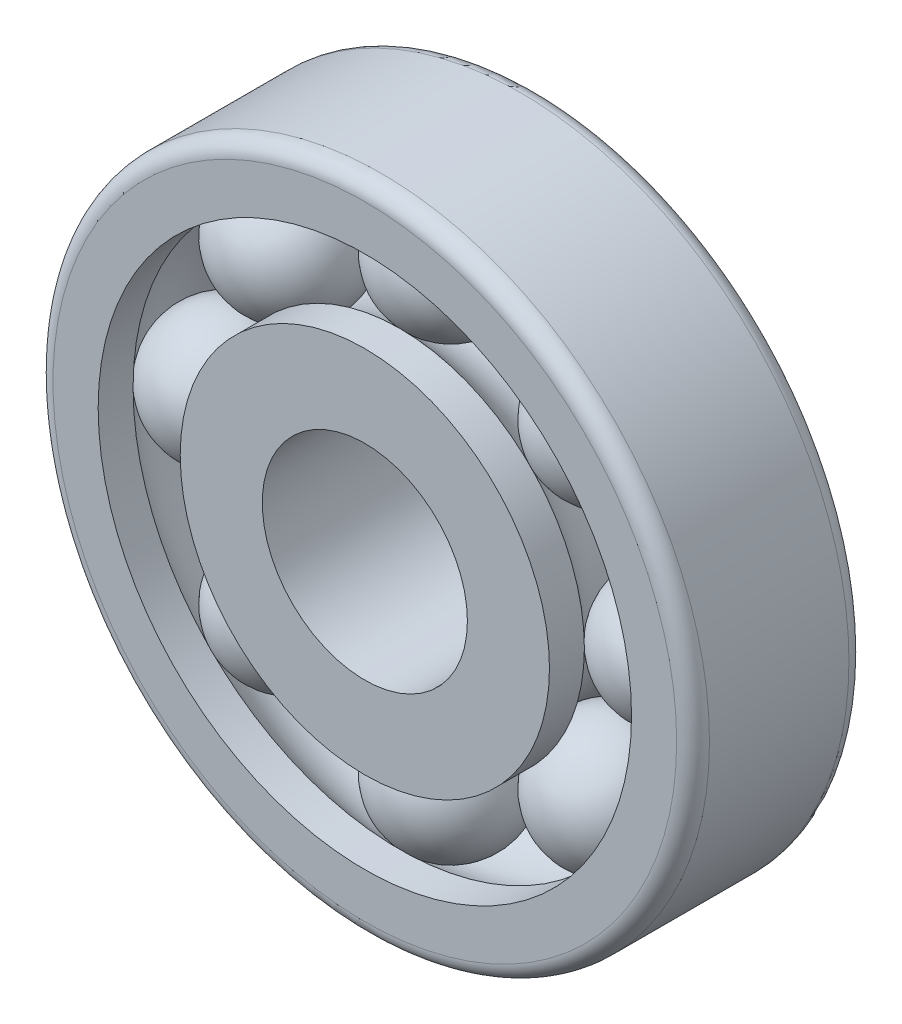
SolidWorks part; units mm, degrees
ref_plane "Front Plane" through (0, 0, 0) normal (0, 0, 1) x (1, 0, 0)
ref_plane "Top Plane" through (0, 0, 0) normal (0, 1, 0) x (1, 0, 0)
ref_plane "Right Plane" through (0, 0, 0) normal (1, 0, 0) x (0, 0, -1)
sketch "Sketch1" plane through (0, 0, 0) normal (0, 0, 1) x (1, 0, 0)
  circle A0 centre (0, 0) radius 12.5
  circle A1 centre (0, 0) radius 22.5
  circle A2 centre (0, 0) radius 32.5
  circle A3 centre (0, 0) radius 40
  dimension "D1" = 80
  dimension "D2" = 65
  dimension "D3" = 45
  dimension "D4" = 25
extrude "Boss-Extrude1" add sketch "Sketch1" along normal blind 21 contours A3 A2 | A1 A0
sketch "Sketch2" plane through (0, 0, 0) normal (0, 1, 0) x (1, 0, 0)
  line L0 (22.5, -10.5) -> (32.5, -10.5) construction
  line L1 (22.5, -21) -> (22.5, 0) construction
  line L2 (32.5, -21) -> (32.5, 0) construction
  line L3 (0, 0) -> (0, 21.9554) construction
  circle A0 centre (27.5, -10.5) radius 8
  dimension "D1" = 16
revolve "Cut-Revolve1" cut sketch "Sketch2" angle 360 about L3
sketch "Sketch3" plane through (0, 0, 0) normal (0, 1, 0) x (1, 0, 0)
  line L0 (27.5, -2.5) -> (27.5, -18.5)
  arc A0 (27.5, -18.5) -> (27.5, -2.5) centre (27.5, -10.5) ccw
  dimension "D1" = 16
revolve "Revolve1" add sketch "Sketch3" angle 360 about L0
pattern_circular "CirPattern1" count 8 over 360 about axis through (0, 0, 0) along (0, 0, 1) of bodies 105
fillet "Fillet1" radius 2 2 edges at (40, 0, 21) (40, 0, 0)
